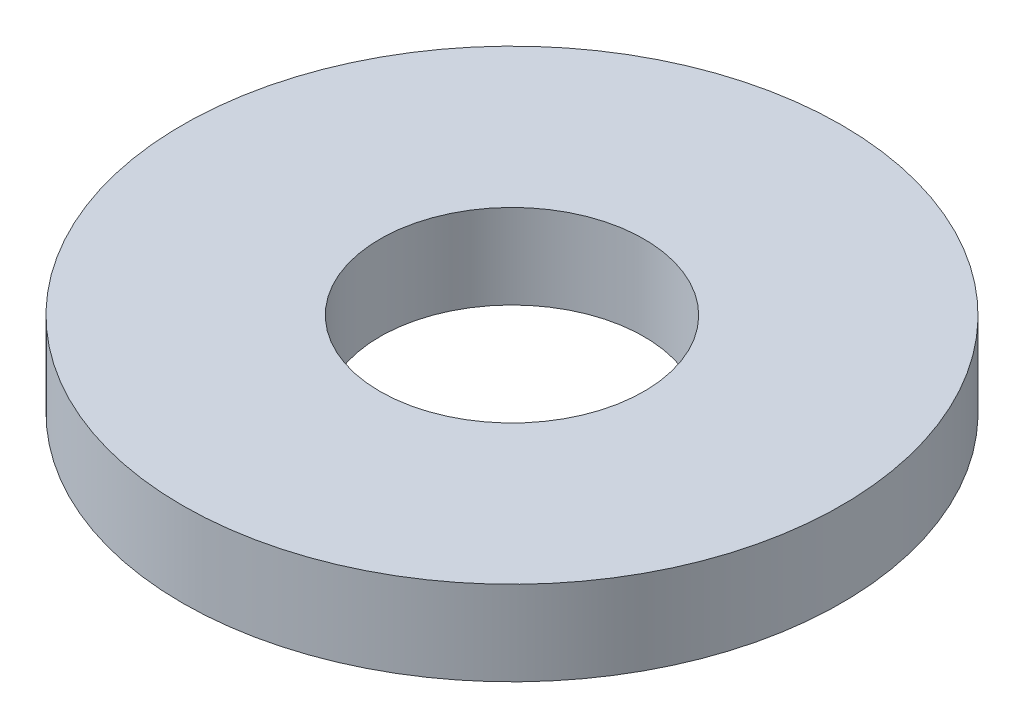
SolidWorks part; units mm, degrees
ref_plane "Front Plane" through (0, 0, 0) normal (0, 0, 1) x (1, 0, 0)
ref_plane "Top Plane" through (0, 0, 0) normal (0, 1, 0) x (1, 0, 0)
ref_plane "Right Plane" through (0, 0, 0) normal (1, 0, 0) x (0, 0, -1)
sketch "Sketch1" plane through (0, 0, 0) normal (0, 1, 0) x (1, 0, 0)
  circle A0 centre (0, 0) radius 3.9624
  dimension "OD" = 7.9248
extrude "Boss-Extrude1" add sketch "Sketch1" along normal blind 1.016
sketch "Sketch5" plane through (0, 1.016, 0) normal (0, 1, 0) x (-1, 0, 0)
  circle A0 centre (0, 0) radius 1.5875
  dimension "ID" = 3.175
extrude "Cut-Extrude1" cut sketch "Sketch5" against normal through all
